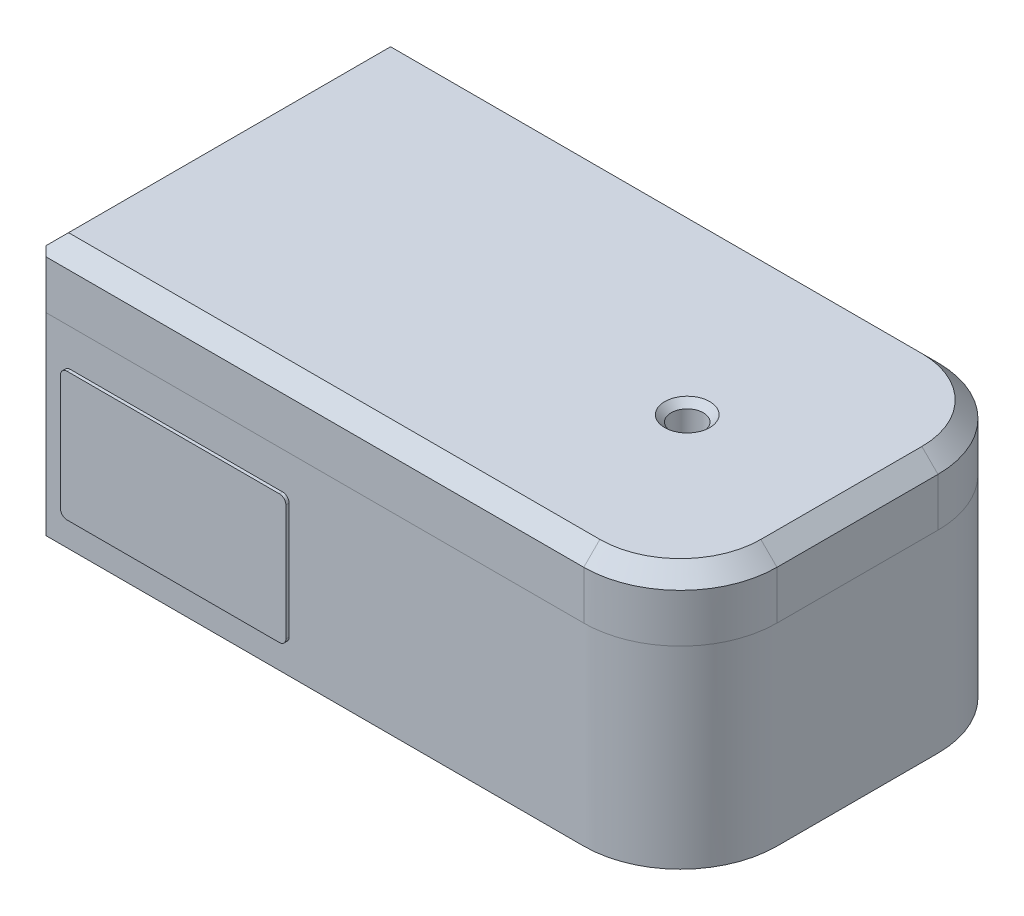
SolidWorks part; units mm, degrees
ref_plane "Front Plane" through (0, 0, 0) normal (0, 0, 1) x (1, 0, 0)
ref_plane "Top Plane" through (0, 0, 0) normal (0, 1, 0) x (1, 0, 0)
ref_plane "Right Plane" through (0, 0, 0) normal (1, 0, 0) x (0, 0, -1)
sketch "Sketch1" plane through (0, 0, 0) normal (0, 1, 0) x (1, 0, 0)
  line L1 (-77.2543, 54.3642) -> (122.7457, 54.3642)
  line L2 (-77.2543, 54.3642) -> (-77.2543, -55.6358)
  line L3 (-77.2543, -55.6358) -> (122.7457, -55.6358)
  line L4 (122.7457, 54.3642) -> (122.7457, -55.6358)
  dimension "D1" = 110
  dimension "D2" = 200
extrude "Boss-Extrude1" add sketch "Sketch1" along normal blind 20
fillet "Fillet2" radius 30 2 edges at (122.7457, 10, -54.3642) (122.7457, 10, 55.6358)
ref_plane "Plane1" through (0, -60, 0) normal (0, -1, 0) x (-1, 0, 0)
sketch "Sketch4" plane through (0, -60, 0) normal (0, -1, 0) x (-1, 0, 0)
  line L3 (-122.7457, 24.3642) -> (-122.7457, -25.6358)
  line L4 (77.2543, 54.3642) -> (-92.7457, 54.3642)
  line L5 (-122.7457, 24.3642) -> (-122.7457, -25.6358)
  line L6 (-92.7457, -55.6358) -> (77.2543, -55.6358)
  line L7 (77.2543, -55.6358) -> (77.2543, 54.3642)
  line L8 (77.2543, 54.3642) -> (-92.7457, 54.3642)
  line L10 (-92.7457, -55.6358) -> (77.2543, -55.6358)
  line L11 (77.2543, -55.6358) -> (77.2543, 54.3642)
  arc A0 (-122.7457, -25.6358) -> (-92.7457, -55.6358) centre (-92.7457, -25.6358) ccw
  arc A1 (-92.7457, 54.3642) -> (-122.7457, 24.3642) centre (-92.7457, 24.3642) ccw
  arc A2 (-92.7457, 54.3642) -> (-122.7457, 24.3642) centre (-92.7457, 24.3642) ccw
  arc A3 (-122.7457, -25.6358) -> (-92.7457, -55.6358) centre (-92.7457, -25.6358) ccw
  point P2 (-122.7457, -54.0809)
  dimension "D3" = 30
  dimension "D2" = 200
  dimension "D1" = 0
loft "Loft1" add profiles "Sketch4" section "Sketch4" section face at (48.1501, 0, 0.6358)
sketch "Sketch2" plane through (0, 20, 0) normal (0, 1, 0) x (1, 0, 0)
  line L0 (-77.2543, 54.3642) -> (-77.2543, -55.6358) construction
  circle A0 centre (72.7457, -3.5059) radius 50
  circle A1 centre (72.7457, -3.5059) radius 5
  dimension "D2" = 100
  dimension "D3" = 10
  dimension "D1" = 150
extrude "Cut-Extrude1" cut sketch "Sketch2" against normal blind 24 contours A1
chamfer "Chamfer1" distance 5 angle 45 6 edges at (113.9589, 20, 46.849) (7.7457, 20, 55.6358) (-77.2543, 20, 0.6358) (7.7457, 20, -54.3642) (113.9589, 20, -45.5774) (122.7457, 20, 0.6358)
sketch "Sketch5" plane through (0, 0, 55.6358) normal (0, 0, 1) x (1, 0, 0)
  line L0 (-77.2543, -60) -> (-77.2543, 0) construction
  line L1 (-66.7543, -51.5) -> (-0.7543, -51.5)
  line L2 (-68.7543, -49.5) -> (-68.7543, -13.5)
  line L3 (-66.7543, -11.5) -> (-0.7543, -11.5)
  line L4 (1.2457, -49.5) -> (1.2457, -13.5)
  line L5 (92.7457, -60) -> (-77.2543, -60) construction
  arc A0 (-66.7543, -51.5) -> (-68.7543, -49.5) centre (-66.7543, -49.5) cw
  arc A1 (-0.7543, -51.5) -> (1.2457, -49.5) centre (-0.7543, -49.5) ccw
  arc A2 (-0.7543, -11.5) -> (1.2457, -13.5) centre (-0.7543, -13.5) cw
  arc A3 (-68.7543, -13.5) -> (-66.7543, -11.5) centre (-66.7543, -13.5) cw
  point P12 (1.2457, -51.5)
  point P15 (1.2457, -11.5)
  dimension "D5" = 2
  dimension "D1" = 8.5
  dimension "D2" = 8.5
  dimension "D3" = 70
  dimension "D4" = 40
extrude "Boss-Extrude2" add sketch "Sketch5" along normal blind 1 contours A3 L2 A0 L1 A1 L4 A2 L3
sketch "Sketch6" plane through (-77.2543, 0, 0) normal (-1, 0, 0) x (0, 0, 1)
  line L0 (65.6358, 0) -> (65.6358, 25)
  line L1 (65.6358, 25) -> (-64.3642, 25)
  line L2 (-64.3642, 25) -> (-64.3642, 0)
  line L3 (-64.3642, 0) -> (-64.3642, -70)
  line L4 (-64.3642, -70) -> (65.6358, -70)
  line L5 (65.6358, -70) -> (65.6358, 0)
  line L6 (55.6358, 0) -> (55.6358, 15)
  line L7 (55.6358, 15) -> (-54.3642, 15)
  line L8 (-54.3642, 15) -> (-54.3642, 0)
  line L9 (-54.3642, 0) -> (-54.3642, -60)
  line L10 (-54.3642, -60) -> (55.6358, -60)
  line L11 (55.6358, -60) -> (55.6358, 0)
  line L12 (55.6358, 0) -> (55.6358, 15) construction
  line L13 (55.6358, 15) -> (-54.3642, 15) construction
  line L14 (-54.3642, 15) -> (-54.3642, 0) construction
  line L15 (-54.3642, 0) -> (-54.3642, -60) construction
  line L16 (-54.3642, -60) -> (55.6358, -60) construction
  line L17 (55.6358, -60) -> (55.6358, 0) construction
  line L19 (40.6358, 5) -> (-39.3642, 5)
  line L21 (-44.3642, 0) -> (-44.3642, -50)
  line L22 (-44.3642, -50) -> (45.6358, -50)
  line L23 (45.6358, -50) -> (45.6358, 0)
  arc A0 (45.6358, 0) -> (40.6358, 5) centre (40.6358, 0) ccw
  arc A1 (-39.3642, 5) -> (-44.3642, 0) centre (-39.3642, 0) ccw
  point P15 (45.6358, 4.6061)
  point P18 (-44.3642, 0)
  point P19 (-44.3642, 0)
  point P20 (0, 0)
  point P21 (0, 0)
  point P22 (-44.3642, 4.7285)
  dimension "D3" = 5
  dimension "D1" = 0
  dimension "D2" = 10
extrude "Cut-Extrude2" cut sketch "Sketch6" against normal blind 5 contours L19 A1 L21 L22 L23 A0
chamfer "Chamfer2" distance 1 angle 45 6 edges at (-77.2543, -50, 0.6358) (-77.2543, -25, 45.6358) (-77.2543, -25, -44.3642) (-77.2543, 3.5355, 44.1714) (-77.2543, 3.5355, -42.8997) (-77.2543, 5, 0.6358)
chamfer "Chamfer3" distance 2 angle 45 1 edges at (72.7457, 20, 8.5059)
chamfer "Chamfer4" distance 3 angle 45 4 edges at (-77.2543, 7.5, 55.6358) (-77.2543, 7.5, -54.3642)
sketch "Sketch9" plane through (0, 0, 56.6358) normal (0, 0, 1) x (1, 0, 0)
  line L0 (-65.7543, -20.5) -> (-61.7224, -14.5)
  line L1 (-65.7543, -14.5) -> (-1.553, -14.5)
  line L2 (-65.7543, -14.5) -> (-65.7543, -20.5)
  line L3 (-65.7543, -20.5) -> (-1.553, -20.5)
  line L4 (-1.553, -14.5) -> (-1.553, -20.5)
  line L5 (-65.7543, -22.5) -> (-1.6626, -22.5)
  line L6 (-65.7543, -22.5) -> (-65.7543, -43.5)
  line L7 (-65.7543, -43.5) -> (-1.6626, -43.5)
  line L8 (-1.6626, -22.5) -> (-1.6626, -43.5)
  line L9 (-65.7543, -45.5) -> (-1.6626, -45.5)
  line L10 (-65.7543, -45.5) -> (-65.7543, -48.5)
  line L11 (-65.7543, -48.5) -> (-1.6626, -48.5)
  line L12 (-1.6626, -45.5) -> (-1.6626, -48.5)
  line L13 (-61.7224, -14.5) -> (-59.4232, -14.5)
  line L14 (-59.4232, -14.5) -> (-59.4232, -20.5)
  line L15 (-59.4232, -20.5) -> (-60.9232, -20.5)
  line L16 (-60.9232, -20.5) -> (-60.9232, -17.5338)
  line L17 (-60.9232, -17.5338) -> (-61.9539, -17.5338)
  line L18 (-61.9539, -17.5338) -> (-63.9471, -20.5)
  line L19 (-63.9471, -20.5) -> (-65.7543, -20.5)
  line L20 (-60.9232, -16.5338) -> (-60.9232, -16)
  line L21 (-60.9232, -16) -> (-61.2819, -16.5338)
  line L22 (-60.9232, -16.5338) -> (-61.2819, -16.5338)
  line L23 (-58.4232, -14.5) -> (-58.4232, -20.5)
  line L24 (-58.4232, -20.5) -> (-56.9232, -20.5)
  line L25 (-56.9232, -20.5) -> (-56.9232, -18.711)
  line L26 (-56.9232, -18.711) -> (-55.6416, -20.5)
  line L27 (-55.6416, -20.5) -> (-53.7963, -20.5)
  line L28 (-53.7963, -20.5) -> (-55.5632, -18.0338)
  line L29 (-58.4232, -14.5) -> (-55.5632, -14.5)
  line L30 (-56.9232, -16.5338) -> (-56.9232, -16)
  line L31 (-68.7543, -49.5) -> (-68.7543, -13.5) construction
  line L32 (-66.7543, -11.5) -> (-0.7543, -11.5) construction
  line L33 (-66.7543, -51.5) -> (-0.7543, -51.5) construction
  line L34 (-55.5632, -16.5338) -> (-56.9232, -16.5338)
  line L35 (-55.5632, -16) -> (-56.9232, -16)
  line L36 (-52.7963, -20.5) -> (-52.7963, -14.5)
  line L37 (-52.7963, -14.5) -> (-51.0534, -14.5)
  line L38 (-51.0534, -14.5) -> (-49.9455, -16.2037)
  line L39 (-49.9455, -16.2037) -> (-48.8011, -14.5)
  line L40 (-48.8011, -14.5) -> (-47.1416, -14.5)
  line L41 (-47.1416, -14.5) -> (-47.1416, -20.5)
  line L42 (-47.1416, -20.5) -> (-48.6416, -20.5)
  line L43 (-48.6416, -20.5) -> (-48.6416, -16.9528)
  line L44 (-48.6416, -16.9528) -> (-49.9658, -18.924)
  line L45 (-49.9658, -18.924) -> (-51.2963, -16.878)
  line L46 (-51.2963, -16.878) -> (-51.2963, -20.5)
  line L47 (-51.2963, -20.5) -> (-52.7963, -20.5)
  line L48 (-46.1416, -14.5) -> (-46.1416, -20.5)
  line L49 (-46.1416, -20.5) -> (-41.6416, -20.5)
  line L50 (-41.6416, -20.5) -> (-41.6416, -19.5)
  line L51 (-41.6416, -19.5) -> (-44.6416, -19.5)
  line L52 (-44.6416, -19.5) -> (-44.6416, -18)
  line L53 (-44.6416, -18) -> (-43.1416, -18)
  line L54 (-43.1416, -18) -> (-43.1416, -17)
  line L55 (-43.1416, -17) -> (-44.6416, -17)
  line L56 (-44.6416, -17) -> (-44.6416, -15.5)
  line L57 (-44.6416, -15.5) -> (-41.6416, -15.5)
  line L58 (-41.6416, -15.5) -> (-41.6416, -14.5)
  line L59 (-41.6416, -14.5) -> (-46.1416, -14.5)
  line L60 (-38.8748, -17.5338) -> (-37.3748, -17.5338)
  line L61 (-38.8748, -14.5) -> (-37.3748, -14.5)
  line L62 (-38.8748, -20.5) -> (-37.3748, -20.5)
  line L63 (-38.8748, -18.0338) -> (-37.3748, -18.0338)
  line L64 (-38.8748, -17.0338) -> (-37.3748, -17.0338)
  line L65 (-38.8748, -15.5) -> (-37.3748, -15.5)
  line L66 (-38.8748, -19.5) -> (-37.3748, -19.5)
  line L67 (-37.3748, -14.5) -> (-37.3748, -15.5)
  line L68 (-38.8748, -19.5) -> (-38.8748, -20.5)
  line L69 (-30.3748, -14.5) -> (-28.8748, -14.5)
  line L70 (-34.6416, -14.5) -> (-33.1416, -14.5)
  line L71 (-34.6416, -14.5) -> (-34.6416, -20.5)
  line L72 (-34.6416, -20.5) -> (-33.1416, -20.5)
  line L73 (-33.1416, -14.5) -> (-33.1416, -20.5)
  line L74 (-30.3748, -20.5) -> (-28.8748, -20.5)
  line L75 (-30.3748, -18.0338) -> (-28.8748, -18.0338)
  line L76 (-30.3748, -17.0338) -> (-28.8748, -17.0338)
  line L77 (-30.3748, -15.5) -> (-28.8748, -15.5)
  line L78 (-30.3748, -19.5) -> (-28.8748, -19.5)
  line L79 (-28.8748, -14.5) -> (-28.8748, -15.5)
  line L80 (-30.3748, -19.5) -> (-30.3748, -20.5)
  arc A0 (-55.5632, -18.0338) -> (-55.5632, -14.5) centre (-55.5632, -16.2669) ccw
  arc A2 (-55.5632, -16.5338) -> (-55.5632, -16) centre (-55.5632, -16.2669) ccw
  arc A3 (-38.8748, -15.5) -> (-38.8748, -17.0338) centre (-38.8748, -16.2669) ccw
  arc A4 (-38.8748, -14.5) -> (-38.8748, -18.0338) centre (-38.8748, -16.2669) ccw
  arc A5 (-37.3748, -18.0338) -> (-37.3748, -19.5) centre (-37.3748, -18.7669) cw
  arc A6 (-37.3748, -17.0338) -> (-37.3748, -20.5) centre (-37.3748, -18.7669) cw
  arc A7 (-30.3748, -15.5) -> (-30.3748, -17.0338) centre (-30.3748, -16.2669) ccw
  arc A8 (-30.3748, -14.5) -> (-30.3748, -18.0338) centre (-30.3748, -16.2669) ccw
  arc A9 (-28.8748, -18.0338) -> (-28.8748, -19.5) centre (-28.8748, -18.7669) cw
  arc A10 (-28.8748, -17.0338) -> (-28.8748, -20.5) centre (-28.8748, -18.7669) cw
  text T0 "<b><i>TECHNOLOGIES</i></b>" font "Century Gothic" height in points 8
  point P41 (-53.7963, -16.2669)
  point P85 (-40.6416, -16.2669)
  point P90 (-35.6416, -18.7669)
  point P107 (-32.1416, -16.2669)
  dimension "D43" = 1
  dimension "D44" = 1
  dimension "D1" = 1.5
  dimension "D2" = 1.5
  dimension "D3" = 1
  dimension "D4" = 1.5
  dimension "D5" = 1.5
  dimension "D6" = 1
  dimension "D7" = 6
  dimension "D9" = 3
  dimension "D10" = 3
  dimension "D11" = 3
  dimension "D12" = 2
  dimension "D13" = 2
  dimension "D14" = 3
  dimension "D15" = 3
  dimension "D16" = 3
  dimension "D17" = 1.5
  dimension "D19" = 1
  dimension "D20" = 1.5
  dimension "D21" = 1.5
  dimension "D22" = 1.5
  dimension "D23" = 1.5
  dimension "D24" = 1
  dimension "D25" = 1
  dimension "D26" = 1.5
  dimension "D27" = 1.5
  dimension "D28" = 1
  dimension "D29" = 1.5
  dimension "D30" = 1.5
  dimension "D31" = 1.5
  dimension "D32" = 1.5
  dimension "D37" = 1.5
  dimension "D38" = 1.5
  dimension "D39" = 1.5
  dimension "D40" = 1
  dimension "D41" = 1.5
  dimension "D42" = 1
  dimension "D45" = 1
  dimension "D18" = 1.5
  dimension "D33" = 0.5
  dimension "D34" = 0.5
  dimension "D35" = 1
  dimension "D36" = 1
extrude "Cut-Extrude3" [suppressed] cut sketch "Sketch9" against normal blind 0.2
